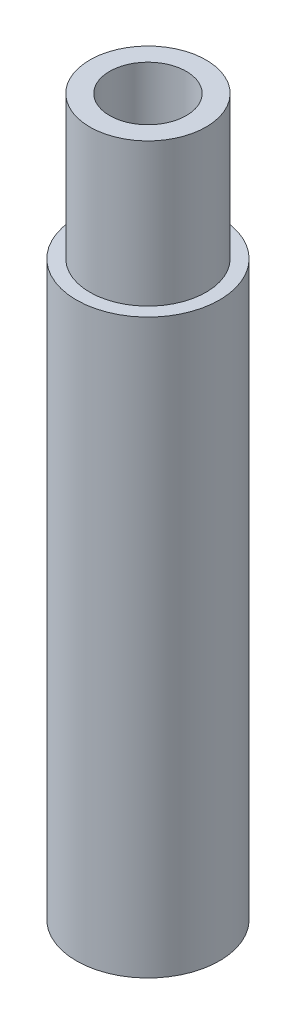
SolidWorks part; units mm, degrees
ref_plane "Front Plane" through (0, 0, 0) normal (0, 0, 1) x (1, 0, 0)
ref_plane "Top Plane" through (0, 0, 0) normal (0, 1, 0) x (1, 0, 0)
ref_plane "Right Plane" through (0, 0, 0) normal (1, 0, 0) x (0, 0, -1)
sketch "Sketch1" plane through (0, 0, 0) normal (0, 1, 0) x (1, 0, 0)
  circle A0 centre (0, 0) radius 3.175
  circle A1 centre (0, 0) radius 1.7018
  dimension "D1" = 3.4036
  dimension "D2" = 6.35
extrude "Extrude1" add sketch "Sketch1" along normal blind 31.75
sketch "Sketch2" plane through (0, 31.75, 0) normal (0, 1, 0) x (-1, 0, 0)
  circle A0 centre (0, 0) radius 3.175 construction
  circle A1 centre (0, 0) radius 3.175
  circle A2 centre (0, 0) radius 2.5797
  dimension "D1" = 5.1594
extrude "Cut-Extrude1" cut sketch "Sketch2" against normal blind 6.35
